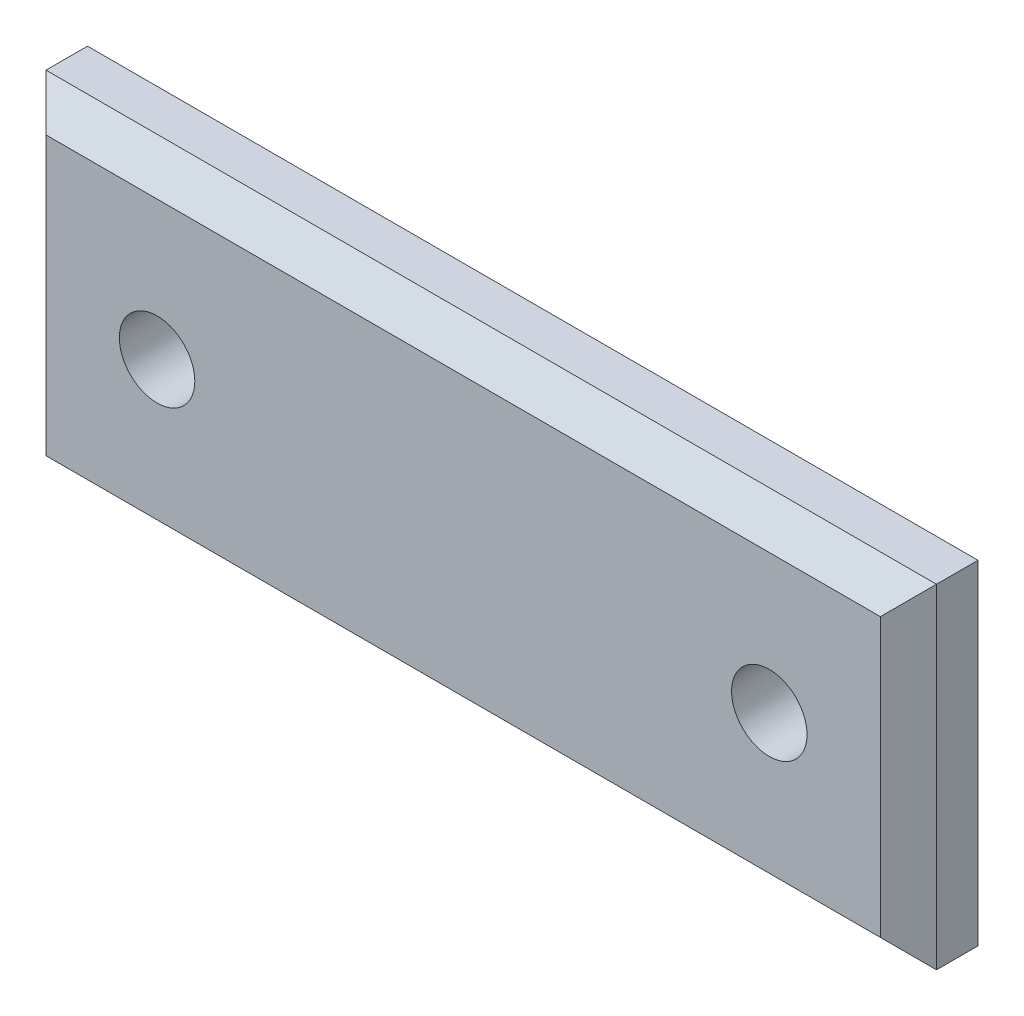
SolidWorks part; units mm, degrees
material "Copper"
ref_plane "Front Plane" through (0, 0, 0) normal (0, 0, 1) x (1, 0, 0)
ref_plane "Top Plane" through (0, 0, 0) normal (0, 1, 0) x (1, 0, 0)
ref_plane "Right Plane" through (0, 0, 0) normal (1, 0, 0) x (0, 0, -1)
sketch "Sketch2" plane through (0, 0, 0) normal (0, 0, 1) x (1, 0, 0)
  line L1 (-25.4, -9.525) -> (25.4, -9.525)
  line L2 (-25.4, -9.525) -> (-25.4, 9.525)
  line L3 (-25.4, 9.525) -> (25.4, 9.525)
  line L4 (25.4, -9.525) -> (25.4, 9.525)
  line L5 (-25.4, -9.525) -> (25.4, 9.525) construction
  line L6 (-25.4, 9.525) -> (25.4, -9.525) construction
  point P0 (0, 0)
  dimension "D1" = 50.8
  dimension "D2" = 19.05
extrude "Boss-Extrude1" add sketch "Sketch2" along normal blind 3.9688
hole_wizard "#8 Clearance Hole1" positions "Sketch3" profile "Sketch4" hole size "#8" standard "ANSI Inch" end condition through all
sketch "Sketch3" plane through (0, 0, 3.9688) normal (0, 0, 1) x (1, 0, 0)
  line L0 (0, 9.525) -> (0, -9.525) construction
  line L1 (25.4, 9.525) -> (-25.4, 9.525) construction
  line L2 (-25.4, -9.525) -> (25.4, -9.525) construction
  line L3 (-25.4, 0) -> (25.4, 0) construction
  line L4 (-25.4, 9.525) -> (-25.4, -9.525) construction
  line L5 (25.4, -9.525) -> (25.4, 9.525) construction
  point P0 (-17.4625, 0)
  point P2 (17.4625, 0)
sketch "Sketch4" plane through (-17.4625, 0, 3.9688) normal (1, 0, 0) x (0, -1, 0)
  line L0 (0, 0) -> (0, 3.9688)
  line L1 (0, 3.9688) -> (2.1526, 3.9688)
  line L2 (2.1526, 3.9688) -> (2.1526, 0)
  line L5 (2.1526, 0) -> (0, 0)
  line L11 (0, -6.35) -> (0, 107.95) construction
  dimension "Thru Hole Dia." = 4.3053
  dimension "Thru Hole Depth" = 3.9688
chamfer "Chamfer1" distance 1.6002 angle 45 4 edges at (0, -9.525, 3.9688) (25.4, 0, 3.9688) (0, 9.525, 3.9688) (-25.4, 0, 3.9688)
equation "\"D2@Sketch3\"=\"D1@Sketch3\""
